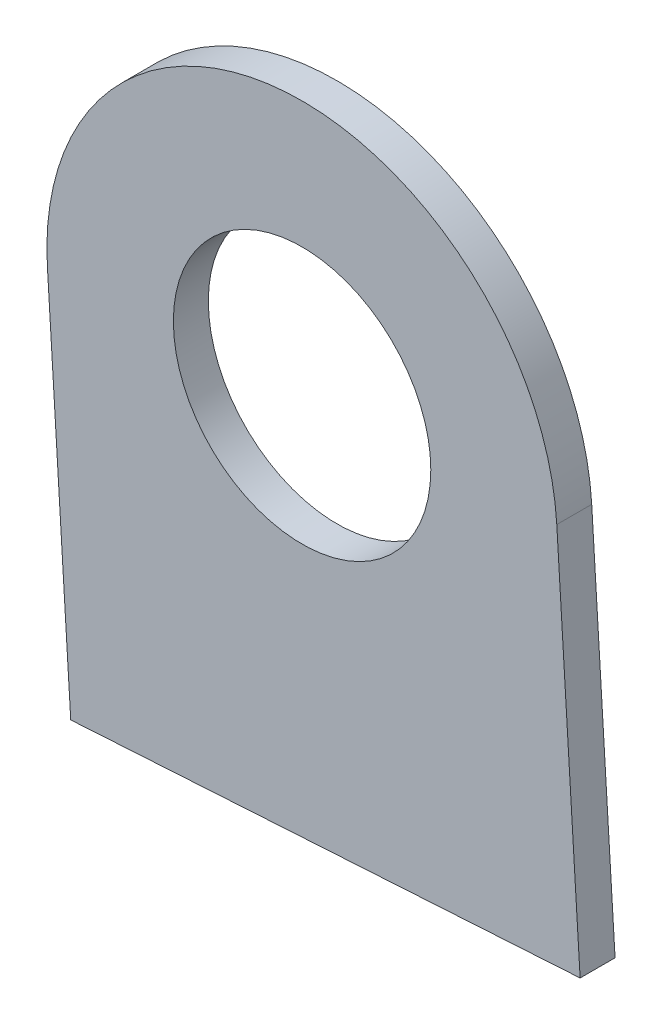
SolidWorks part; units mm, degrees
ref_plane "Front Plane" through (0, 0, 0) normal (0, 0, 1) x (1, 0, 0)
ref_plane "Top Plane" through (0, 0, 0) normal (0, 1, 0) x (1, 0, 0)
ref_plane "Right Plane" through (0, 0, 0) normal (1, 0, 0) x (0, 0, -1)
sketch "Sketch2" plane through (0, 0, 777.3619) normal (0, 0, 1) x (1, 0, 0)
  line L1 (-21.8644, -1.3397) -> (-19.8599, -34.0518)
  line L2 (21.8644, 1.3397) -> (23.8688, -31.3723)
  line L3 (-19.8599, -34.0518) -> (23.8688, -31.3723)
  arc A0 (21.8644, 1.3397) -> (-21.8644, -1.3397) centre (0, 0) ccw
  circle A2 centre (0, 0) radius 11.05
extrude "Boss-Extrude1" add sketch "Sketch2" along normal blind 3
